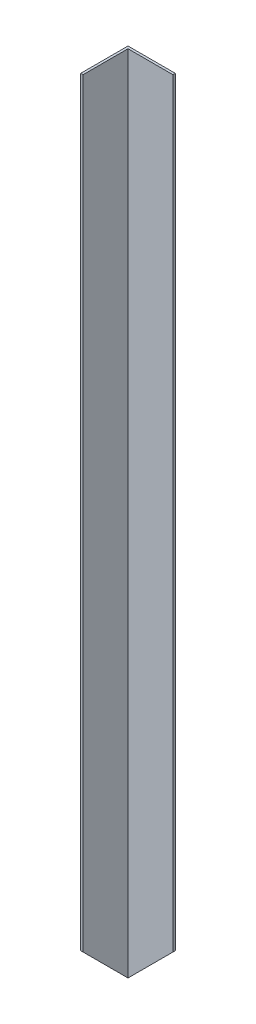
SolidWorks part; units mm, degrees
ref_plane "Plan de face" through (0, 0, 0) normal (0, 0, 1) x (1, 0, 0)
ref_plane "Plan de dessus" through (0, 0, 0) normal (0, 1, 0) x (1, 0, 0)
ref_plane "Plan de droite" through (0, 0, 0) normal (1, 0, 0) x (0, 0, -1)
sketch "Esquisse1" plane through (0, 0, 0) normal (0, 1, 0) x (1, 0, 0)
  line L1 (-20, 20.1136) -> (20, 20.1136)
  line L2 (-20, 20.1136) -> (-20, -19.8864)
  line L3 (-20, -19.8864) -> (-18, -19.8864)
  line L4 (20, 20.1136) -> (20, 18.1136)
  line L5 (-18, 18.1136) -> (20, 18.1136)
  line L6 (-18, 18.1136) -> (-18, -19.8864)
  dimension "D1" = 20
  dimension "D2" = 40
  dimension "D3" = 40
  dimension "D4" = 2
  dimension "D5" = 2
extrude "Boss.-Extru.1" add sketch "Esquisse1" along normal blind 682
sketch "Esquisse2" plane through (0, 0, -20.1136) normal (0, 0, -1) x (-1, 0, 0)
  line L0 (20, 0) -> (-20, 40)
  line L1 (20, 0) -> (-20, 0)
  line L2 (-20, 0) -> (-20, 40)
  dimension "D1" = 45
extrude "Enlèv. mat.-Extru.1" cut sketch "Esquisse2" against normal blind 590
sketch "Esquisse3" plane through (-20, 0, 0) normal (-1, 0, 0) x (0, 0, 1)
  line L0 (-20.1136, 0) -> (19.8864, 40)
  line L1 (19.8864, 682) -> (19.8864, 0) construction
  line L2 (19.8864, 40) -> (19.8864, 0)
  line L3 (19.8864, 0) -> (-20.1136, 0)
  dimension "D1" = 45
extrude "Enlèv. mat.-Extru.2" cut sketch "Esquisse3" against normal blind 590
